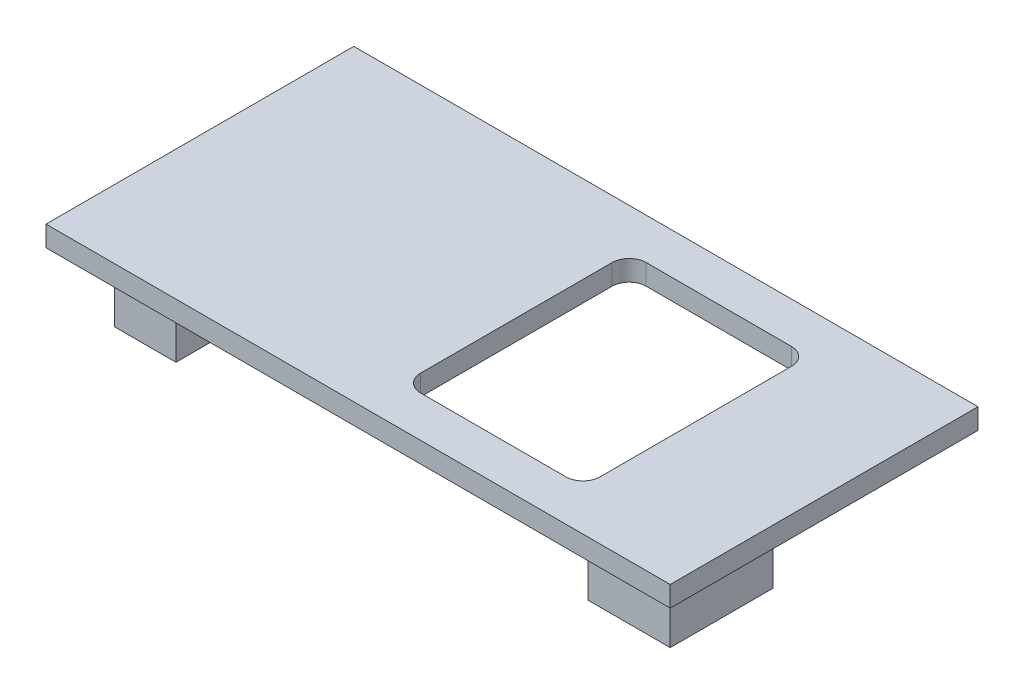
SolidWorks part; units mm, degrees
ref_plane "Front Plane" through (0, 0, 0) normal (0, 0, 1) x (1, 0, 0)
ref_plane "Top Plane" through (0, 0, 0) normal (0, 1, 0) x (1, 0, 0)
ref_plane "Right Plane" through (0, 0, 0) normal (1, 0, 0) x (0, 0, -1)
sketch "Sketch1" plane through (0, 0, 0) normal (0, 1, 0) x (1, 0, 0)
  line L0 (0, 0) -> (36.5, 0)
  line L1 (0, 0) -> (0, 18)
  line L2 (0, 18) -> (36.5, 18)
  line L3 (36.5, 0) -> (36.5, 18)
  point P4 (0, 0)
  point P5 (0, 0)
  dimension "D1" = 36.5
  dimension "D2" = 18
extrude "Boss-Extrude1" add sketch "Sketch1" along normal blind 1.2
sketch "Sketch2" plane through (0, 0, 0) normal (0, -1, 0) x (1, 0, 0)
  line L0 (0, 0) -> (36.5, 0) construction
  line L1 (2, -2) -> (5.6, -2)
  line L2 (2, -2) -> (2, -7)
  line L3 (2, -7) -> (5.6, -7)
  line L4 (5.6, -2) -> (5.6, -7)
  line L5 (0, -18) -> (0, 0) construction
  line L6 (36.5, 0) -> (36.5, -18) construction
  line L7 (34.5, -2) -> (29.7, -2)
  line L8 (34.5, -2) -> (34.5, -8)
  line L9 (34.5, -8) -> (29.7, -8)
  line L10 (29.7, -2) -> (29.7, -8)
  dimension "D1" = 2
  dimension "D2" = 2
  dimension "D3" = 5
  dimension "D4" = 3.6
  dimension "D5" = 6
  dimension "D6" = 4.8
  dimension "D7" = 2
  dimension "D8" = 2
extrude "Boss-Extrude2" add sketch "Sketch2" along normal blind 4
sketch "Sketch3" plane through (0, 1.2, 0) normal (0, 1, 0) x (1, 0, 0)
  line L0 (0, 18) -> (0, 0) construction
  line L1 (18.5, 15.6) -> (29, 15.6)
  line L2 (18.5, 15.6) -> (18.5, 2.4)
  line L3 (18.5, 2.4) -> (29, 2.4)
  line L4 (29, 15.6) -> (29, 2.4)
  line L5 (36.5, 0) -> (36.5, 18) construction
  line L6 (36.5, 18) -> (0, 18) construction
  line L7 (0, 0) -> (36.5, 0) construction
  dimension "D1" = 18.5
  dimension "D2" = 7.5
  dimension "D3" = 2.4
  dimension "D4" = 2.4
extrude "Cut-Extrude1" cut sketch "Sketch3" against normal up to next
fillet "Fillet1" radius 1 4 edges at (18.5, 0.6, -2.4) (29, 0.6, -2.4) (29, 0.6, -15.6) (18.5, 0.6, -15.6)
